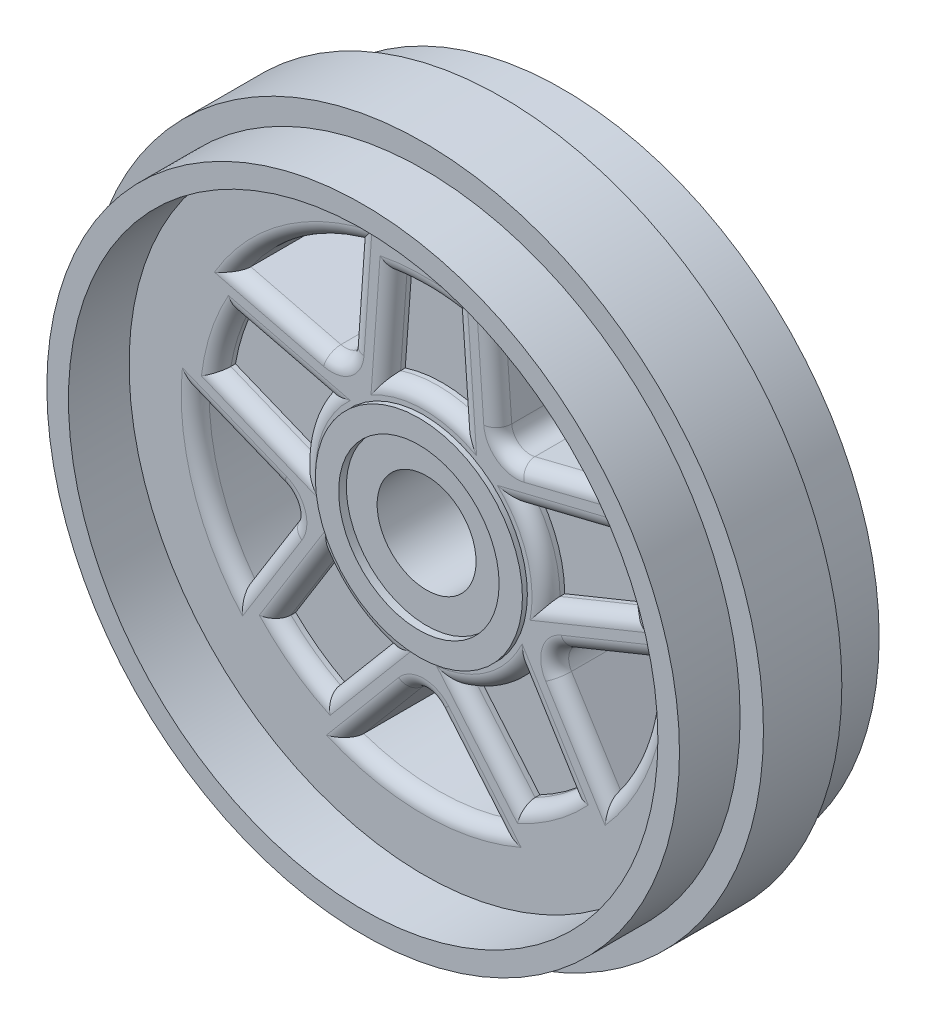
SolidWorks part; units mm, degrees
material "Custom Plastic"
ref_plane "Front Plane" through (0, 0, 0) normal (0, 0, 1) x (1, 0, 0)
ref_plane "Top Plane" through (0, 0, 0) normal (0, 1, 0) x (1, 0, 0)
ref_plane "Right Plane" through (0, 0, 0) normal (1, 0, 0) x (0, 0, -1)
sketch "Sketch1" plane through (0, 0, 0) normal (0, 0, 1) x (1, 0, 0)
  line L0 (0, 8.6106) -> (0, 11.6586)
  line L1 (0, 2.1844) -> (0, 2.8194)
  line L2 (0, 8.0229) -> (0, 7.3879)
  circle A0 centre (0, 0) radius 1.3462
  circle A2 centre (0, 0) radius 8.0229
  circle A3 centre (0, 0) radius 8.6106
  circle A4 centre (0, 0) radius 1.524
  circle A5 centre (0, 0) radius 2.1844
  circle A7 centre (0, 0) radius 2.8194
  circle A9 centre (0, 0) radius 6.223
extrude "Boss-Extrude1" add sketch "Sketch1" against normal blind 5.4356
sketch "Sketch3" plane through (0, 0, 0) normal (0, 0, 1) x (1, 0, 0)
  line L0 (0, 8.6106) -> (0, 9.2456)
  circle A0 centre (0, 0) radius 8.6106 construction
  circle A1 centre (0, 0) radius 9.2456
extrude "Boss-Extrude2" add sketch "Sketch3" against normal through all
sketch "Sketch4" plane through (0, 0, 0) normal (0, 0, 1) x (1, 0, 0)
  circle A0 centre (0, 0) radius 8.6106
  circle A1 centre (0, 0) radius 9.2456
extrude "Cut-Extrude1" cut sketch "Sketch4" against normal blind 1.651
sketch "Sketch5" plane through (0, 0, -5.4356) normal (0, 0, -1) x (-1, 0, 0)
  circle A0 centre (0, 0) radius 9.2456
  circle A1 centre (0, 0) radius 8.6106
extrude "Cut-Extrude2" cut sketch "Sketch5" against normal blind 1.651
sketch "Sketch6" plane through (0, 0, 0) normal (0, 0, 1) x (1, 0, 0)
  circle A1 centre (0, 0) radius 2.8194
  circle A2 centre (0, 0) radius 8.0229
extrude "Cut-Extrude3" cut sketch "Sketch6" against normal blind 1.651
sketch "Sketch7" plane through (0, 0, 0) normal (0, 0, 1) x (1, 0, 0)
  circle A0 centre (0, 0) radius 2.8194
  circle A1 centre (0, 0) radius 2.1844
extrude "Cut-Extrude4" cut sketch "Sketch7" against normal blind 1.5166
sketch "Sketch8" plane through (0, 0, 0) normal (0, 0, 1) x (1, 0, 0)
  circle A1 centre (0, 0) radius 1.524
  circle A2 centre (0, 0) radius 2.1844
extrude "Cut-Extrude5" cut sketch "Sketch8" against normal blind 1.7272
sketch "Sketch9" plane through (0, 0, 0) normal (0, 0, 1) x (1, 0, 0)
  circle A0 centre (0, 0) radius 1.3462
extrude "Cut-Extrude6" cut sketch "Sketch9" against normal through all
sketch "Sketch10" plane through (0, 0, 0) normal (0, 0, 1) x (1, 0, 0)
  circle A0 centre (0, 0) radius 1.3462
  circle A2 centre (0, 0) radius 1.524
extrude "Cut-Extrude7" cut sketch "Sketch10" against normal blind 1.7272
sketch "Sketch11" plane through (0, 0, -1.651) normal (0, 0, 1) x (1, 0, 0)
  line L0 (0, 2.8194) -> (0, 6.223)
  line L1 (1.3389, 5.6908) -> (1.519, 3.2064)
  line L2 (-1.3389, 5.6908) -> (-1.519, 3.2064)
  line L3 (0.8323, 5.6541) -> (1.0123, 3.1697)
  line L4 (-0.8323, 5.6541) -> (-1.0123, 3.1697)
  line L5 (5.826, 0.4852) -> (3.5189, -0.4538)
  line L6 (4.9985, 3.0319) -> (2.5801, 2.4355)
  line L7 (5.6345, 0.9557) -> (3.3274, 0.0167)
  line L8 (5.1202, 2.5387) -> (2.7017, 1.9422)
  line L9 (2.2618, -5.391) -> (0.6558, -3.4869)
  line L10 (4.4282, -3.817) -> (3.1136, -1.7012)
  line L11 (2.6501, -5.0634) -> (1.0441, -3.1593)
  line L12 (3.9967, -4.0851) -> (2.6821, -1.9693)
  line L13 (-4.4282, -3.817) -> (-3.1136, -1.7012)
  line L14 (-2.2618, -5.391) -> (-0.6558, -3.4869)
  line L15 (-3.9967, -4.0851) -> (-2.6821, -1.9693)
  line L16 (-2.6501, -5.0634) -> (-1.0441, -3.1593)
  line L17 (-4.9985, 3.0319) -> (-2.5801, 2.4355)
  line L18 (-5.826, 0.4852) -> (-3.5189, -0.4538)
  line L19 (-5.1202, 2.5387) -> (-2.7017, 1.9422)
  line L20 (-5.6345, 0.9557) -> (-3.3274, 0.0167)
  line L21 (1.8296, 5.948) -> (2.012, 3.4308)
  line L22 (-1.8296, 5.948) -> (-2.0122, 3.4293)
  line L23 (-1.8456, 5.7275) -> (-2.0257, 3.2431) construction
  line L24 (1.8456, 5.7275) -> (2.0257, 3.2431) construction
  line L25 (5.0922, 3.579) -> (2.6404, 2.9743)
  line L26 (6.2229, 0.0989) -> (3.8854, -0.8524)
  line L27 (4.9781, -3.736) -> (3.6454, -1.5911)
  line L28 (2.0177, -5.8868) -> (0.3906, -3.9577)
  line L29 (-2.0141, -5.888) -> (-0.386, -3.9577)
  line L30 (-4.9745, -3.7372) -> (-3.6426, -1.5935)
  line L31 (-6.2215, 0.097) -> (-3.8826, -0.8549)
  line L32 (-5.0908, 3.5771) -> (-2.6405, 2.9728)
  circle A0 centre (0, 0) radius 6.223 construction
  arc A1 (0, 6.223) -> (0.9062, 6.1567) centre (0, 0) cw
  circle A2 centre (0, 0) radius 2.8194 construction
  arc A3 (0, 6.223) -> (-0.9062, 6.1567) centre (0, 0) ccw
  arc A4 (0.8578, 2.6858) -> (-0.8578, 2.6858) centre (0, 0) ccw
  arc A5 (-0.8578, 2.6858) -> (-1.519, 3.2064) centre (-1.0123, 3.1697) cw
  arc A6 (-1.3389, 5.6908) -> (-0.9062, 6.1567) centre (-0.8323, 5.6541) cw
  arc A7 (1.3389, 5.6908) -> (0.9062, 6.1567) centre (0.8323, 5.6541) ccw
  arc A8 (1.519, 3.2064) -> (0.8578, 2.6858) centre (1.0123, 3.1697) cw
  arc A9 (0, 5.715) -> (0.8323, 5.6541) centre (0, 0) cw
  arc A10 (0.8323, 5.6541) -> (0.8323, 5.6541) centre (0.8323, 5.6541) ccw
  arc A11 (1.0123, 3.1697) -> (1.0123, 3.1697) centre (1.0123, 3.1697) cw
  arc A12 (1.0123, 3.1697) -> (-1.0123, 3.1697) centre (0, 0) ccw
  arc A13 (-1.0123, 3.1697) -> (-1.0123, 3.1697) centre (-1.0123, 3.1697) cw
  arc A14 (-0.8323, 5.6541) -> (-0.8323, 5.6541) centre (-0.8323, 5.6541) cw
  arc A15 (0, 5.715) -> (-0.8323, 5.6541) centre (0, 0) ccw
  arc A16 (3.5189, -0.4538) -> (2.8194, 0.0142) centre (3.3274, 0.0167) cw
  arc A17 (5.826, 0.4852) -> (6.1354, 1.0406) centre (5.6345, 0.9557) ccw
  arc A18 (5.9184, 1.923) -> (6.1354, 1.0406) centre (0, 0) cw
  arc A19 (2.8194, 0.0142) -> (2.2892, 1.6457) centre (0, 0) ccw
  arc A20 (2.2892, 1.6457) -> (2.5801, 2.4355) centre (2.7017, 1.9422) cw
  arc A21 (4.9985, 3.0319) -> (5.5753, 2.7644) centre (5.1202, 2.5387) cw
  arc A22 (5.9184, 1.923) -> (5.5753, 2.7644) centre (0, 0) ccw
  arc A23 (5.4353, 1.766) -> (5.1202, 2.5387) centre (0, 0) ccw
  arc A24 (5.4353, 1.766) -> (5.6345, 0.9557) centre (0, 0) cw
  arc A25 (3.3274, 0.0167) -> (2.7017, 1.9422) centre (0, 0) ccw
  arc A26 (0.6558, -3.4869) -> (0.8847, -2.677) centre (1.0441, -3.1593) cw
  arc A27 (2.2618, -5.391) -> (2.8856, -5.5135) centre (2.6501, -5.0634) ccw
  arc A28 (3.6578, -5.0345) -> (2.8856, -5.5135) centre (0, 0) cw
  arc A29 (0.8847, -2.677) -> (2.2726, -1.6686) centre (0, 0) ccw
  arc A30 (2.2726, -1.6686) -> (3.1136, -1.7012) centre (2.6821, -1.9693) cw
  arc A31 (4.4282, -3.817) -> (4.352, -4.4482) centre (3.9967, -4.0851) cw
  arc A32 (3.6578, -5.0345) -> (4.352, -4.4482) centre (0, 0) ccw
  arc A33 (3.3592, -4.6235) -> (3.9967, -4.0851) centre (0, 0) ccw
  arc A34 (3.3592, -4.6235) -> (2.6501, -5.0634) centre (0, 0) cw
  arc A35 (1.0441, -3.1593) -> (2.6821, -1.9693) centre (0, 0) ccw
  arc A36 (-3.1136, -1.7012) -> (-2.2726, -1.6686) centre (-2.6821, -1.9693) cw
  arc A37 (-4.4282, -3.817) -> (-4.352, -4.4482) centre (-3.9967, -4.0851) ccw
  arc A38 (-3.6578, -5.0345) -> (-4.352, -4.4482) centre (0, 0) cw
  arc A39 (-2.2726, -1.6686) -> (-0.8847, -2.677) centre (0, 0) ccw
  arc A40 (-0.8847, -2.677) -> (-0.6558, -3.4869) centre (-1.0441, -3.1593) cw
  arc A41 (-2.2618, -5.391) -> (-2.8856, -5.5135) centre (-2.6501, -5.0634) cw
  arc A42 (-3.6578, -5.0345) -> (-2.8856, -5.5135) centre (0, 0) ccw
  arc A43 (-3.3592, -4.6235) -> (-2.6501, -5.0634) centre (0, 0) ccw
  arc A44 (-3.3592, -4.6235) -> (-3.9967, -4.0851) centre (0, 0) cw
  arc A45 (-2.6821, -1.9693) -> (-1.0441, -3.1593) centre (0, 0) ccw
  arc A46 (-2.5801, 2.4355) -> (-2.2892, 1.6457) centre (-2.7017, 1.9422) cw
  arc A47 (-4.9985, 3.0319) -> (-5.5753, 2.7644) centre (-5.1202, 2.5387) ccw
  arc A48 (-5.9184, 1.923) -> (-5.5753, 2.7644) centre (0, 0) cw
  arc A49 (-2.2892, 1.6457) -> (-2.8194, 0.0142) centre (0, 0) ccw
  arc A50 (-2.8194, 0.0142) -> (-3.5189, -0.4538) centre (-3.3274, 0.0167) cw
  arc A51 (-5.826, 0.4852) -> (-6.1354, 1.0406) centre (-5.6345, 0.9557) cw
  arc A52 (-5.9184, 1.923) -> (-6.1354, 1.0406) centre (0, 0) ccw
  arc A53 (-5.4353, 1.766) -> (-5.6345, 0.9557) centre (0, 0) ccw
  arc A54 (-5.4353, 1.766) -> (-5.1202, 2.5387) centre (0, 0) cw
  arc A55 (-2.7017, 1.9422) -> (-3.3274, 0.0167) centre (0, 0) ccw
  circle A56 centre (0, 0) radius 6.223
  circle A57 centre (0, 0) radius 2.8194
  circle A58 centre (0.0007, 0.001) radius 2.8194
  circle A59 centre (0.0018, 0.0006) radius 2.8194
  circle A60 centre (0.0018, -0.0006) radius 2.8194
  circle A61 centre (0.0007, -0.001) radius 2.8194
  arc A62 (-3.8826, -0.8549) -> (-3.6426, -1.5935) centre (-4.0741, -1.3254) cw
  arc A63 (-0.386, -3.9577) -> (0.3906, -3.9577) centre (0.0023, -4.2852) cw
  arc A64 (3.8854, -0.8524) -> (3.6454, -1.5911) centre (4.0769, -1.323) ccw
  arc A65 (2.6404, 2.9743) -> (2.012, 3.4308) centre (2.5187, 3.4676) cw
  arc A66 (-2.0122, 3.4293) -> (-2.6405, 2.9728) centre (-2.5188, 3.466) cw
  circle A67 centre (0, 0) radius 6.2219
  point P16 (-1.5822, 2.3336)
  point P19 (-1.3105, 6.0835)
  point P22 (1.3105, 6.0835)
  point P25 (1.5822, 2.3336)
  point P133 (0, 0)
  point P150 (0.001, 0)
  dimension "D1" = 0.508
  dimension "D2" = 0.508
  dimension "D8" = 0.508
  dimension "D3" = 0.508
  dimension "D5" = 0.508
  dimension "D6" = 0.508
  dimension "D4" = 5
  dimension "D7" = 5
extrude "Cut-Extrude9" cut sketch "Sketch11" against normal blind 0.508 contours A55 L19 A54 A53 L20 | L0 A15 L4 A12 | A12 L3 A9 L0 | A25 L7 A24 A23 L8 | A35 L11 A34 A33 L12 | A45 L15 A44 A43 L16
sketch "Sketch13" plane through (0, 0, -1.651) normal (0, 0, 1) x (1, 0, 0)
  line L0 (2.0146, -5.8879) -> (0.3855, -3.954)
  line L1 (-2.0146, -5.8879) -> (-0.3921, -3.9548)
  line L2 (-6.2223, 0.0966) -> (-3.8824, -0.8491)
  line L3 (-4.9772, -3.7355) -> (-3.6414, -1.5885)
  line L4 (-1.831, 5.9475) -> (-2.0073, 3.43)
  line L5 (-5.0907, 3.5792) -> (-2.636, 2.9723)
  line L6 (5.0907, 3.5792) -> (2.6418, 2.969)
  line L7 (1.831, 5.9475) -> (2.0123, 3.4255)
  line L8 (4.9772, -3.7355) -> (3.64, -1.595)
  line L9 (6.2223, 0.0966) -> (3.8796, -0.8553)
  circle A0 centre (0, 0) radius 6.223
  arc A1 (0.3855, -3.954) -> (-0.3921, -3.9548) centre (-0.003, -4.2813) ccw
  arc A2 (-3.6414, -1.5885) -> (-3.8824, -0.8491) centre (-4.0727, -1.3201) ccw
  arc A3 (-2.636, 2.9723) -> (-2.0073, 3.43) centre (-2.5141, 3.4655) ccw
  arc A4 (2.0123, 3.4255) -> (2.6418, 2.969) centre (2.519, 3.4619) ccw
  arc A5 (3.8796, -0.8553) -> (3.64, -1.595) centre (4.0709, -1.3259) ccw
  point P31 (0, 0)
  dimension "D1" = 5
extrude "Cut-Extrude10" cut sketch "Sketch13" against normal through all contours L0 A1 L1 A0 | L9 A5 L8 A0 | L7 A4 L6 A0 | L5 A3 L4 A0 | L3 A2 L2 A0
fillet "Fillet1" radius 0.381 40 edges at (1.2, -4.921, -1.651) (-0.0035, -3.7733, -1.651) (-4.3093, -2.662, -1.651) (-3.5897, -1.1627, -1.651) (-3.8633, 3.2758, -1.651) (-2.2151, 3.0548, -1.651) (3.8662, 3.2741, -1.651) (2.2207, 3.0506, -1.651) (5.0509, -0.3794, -1.651) (3.5876, -1.1694, -1.651) (-3.1645, 1.0282, -1.651) (-1.9558, -2.6919, -1.651) (-3.3394, -3.0272, -1.651) (-1.8471, -4.1114, -1.651) (-3.3592, -4.6235, -1.651) (5.4353, 1.766, -1.651) (5.9184, -1.923, -1.651) (3.3592, -4.6235, -1.651) (1.9558, -2.6919, -1.651) (3.1645, 1.0282, -1.651) (0, 3.3274, -1.651) (0, 5.715, -1.651) (-5.4353, 1.766, -1.651) (0, -6.223, -1.651) (-1.2034, -4.9213, -1.651) (3.6578, 5.0345, -1.651) (-3.6578, 5.0345, -1.651) (-5.9184, -1.923, -1.651) (-5.0523, -0.3763, -1.651) (-4.4809, 0.4862, -1.651) (-3.9109, 2.2405, -1.651) (-1.9191, 4.6888, -1.651) (-0.9223, 4.4119, -1.651) (0.9223, 4.4119, -1.651) (1.9216, 4.6865, -1.651) (3.9109, 2.2405, -1.651) (4.4809, 0.4862, -1.651) (4.3086, -2.6652, -1.651) (3.3394, -3.0272, -1.651) (1.8471, -4.1114, -1.651)
sketch "Sketch14" plane through (0, 0, -1.7272) normal (0, 0, 1) x (1, 0, 0)
  circle A0 centre (0, 0) radius 0.762
  circle A1 centre (0, 0) radius 1.3462
  circle A2 centre (0, 0) radius 0.762
  circle A3 centre (0, 0) radius 1.3462
sketch "Sketch15" plane through (0, 0, -1.7272) normal (0, 0, 1) x (1, 0, 0)
  circle A0 centre (0, 0) radius 0.762
  circle A1 centre (0, 0) radius 1.3462
scale "Scale1" bodies to scale 115 scale about centroid uniform scaling yes scale factor 0.5
